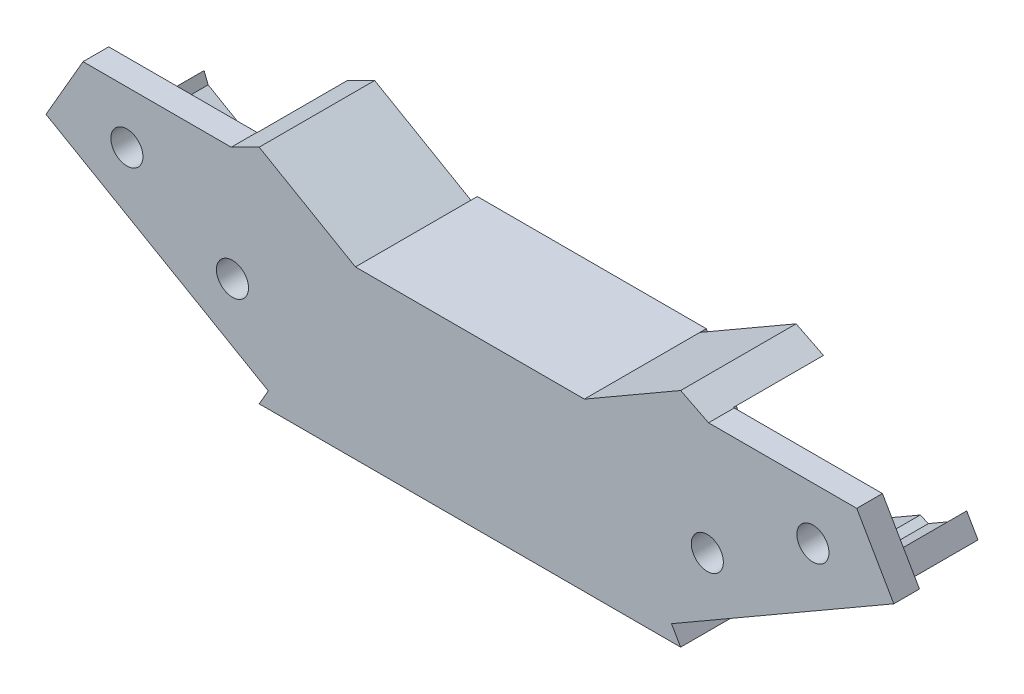
SolidWorks part; units mm, degrees
ref_plane "Alzado" through (0, 0, 0) normal (0, 0, 1) x (1, 0, 0)
ref_plane "Planta" through (0, 0, 0) normal (0, 1, 0) x (1, 0, 0)
ref_plane "Vista lateral" through (0, 0, 0) normal (1, 0, 0) x (0, 0, -1)
sketch "Croquis1" plane through (0, 0, 0) normal (0, 0, 1) x (1, 0, 0)
  line L0 (-8.9198, 0) -> (8.9198, 0)
  line L1 (-8.9198, 0) -> (0, -5.1498) construction
  line L2 (0, -5.1498) -> (8.9198, 0) construction
  line L3 (0, 0) -> (0, -5.1498) construction
  line L4 (8.9198, 0) -> (13.2499, 2.5) construction
  line L5 (8.9198, 0) -> (13.2499, -7.5) construction
  line L6 (8.9198, 0) -> (16.4198, -12.9904)
  line L7 (16.4198, -12.9904) -> (-16.4198, -12.9904)
  line L8 (-8.9198, 0) -> (-16.4198, -12.9904)
  arc A0 (-4.4599, -2.5749) -> (4.4599, -2.5749) centre (0, -5.1498) cw construction
  point P4 (0, 0)
  point P13 (0, -12.9904)
extrude "Saliente-Extruir1" add sketch "Croquis1" along normal blind 7.5
sketch "Croquis2" plane through (0, 0, 7.5) normal (0, 0, 1) x (1, 0, 0)
  line L5 (-18.5961, 3.2401) -> (-9.9358, -1.7599) construction
  line L6 (-8.9198, 0) -> (-16.4198, 4.3301)
  line L7 (-16.4198, 4.3301) -> (-18.5961, 3.2401)
  line L8 (16.4198, -12.9904) -> (8.9198, 0)
  line L9 (8.9198, 0) -> (-8.9198, 0)
  line L10 (-8.9198, 0) -> (-16.4198, -12.9904)
  line L11 (-16.4198, -12.9904) -> (16.4198, -12.9904)
  line L12 (16.4198, -12.9904) -> (15.7093, -11.7599)
  line L13 (8.9198, 0) -> (-8.9198, 0)
  line L14 (-15.7093, -11.7599) -> (-16.4198, -12.9904)
  line L15 (-16.4198, -12.9904) -> (16.4198, -12.9904)
  line L16 (-18.5961, 3.2401) -> (-30.1431, 3.2401)
  line L17 (-32.0563, -0.0737) -> (-27.0063, 8.6731) construction
  line L18 (-30.1431, 3.2401) -> (-33.0298, -1.7599)
  line L19 (-33.0298, -1.7599) -> (-15.7093, -11.7599)
  line L20 (0, 0) -> (0, -12.9904) construction
  line L21 (33.0298, -1.7599) -> (15.7093, -11.7599)
  line L22 (30.1431, 3.2401) -> (33.0298, -1.7599)
  line L23 (8.9198, 0) -> (16.4198, 4.3301)
  line L24 (16.4198, 4.3301) -> (18.5961, 3.2401)
  line L25 (18.5961, 3.2401) -> (30.1431, 3.2401)
  circle A0 centre (-26.7262, -0.8417) radius 1.25
  circle A1 centre (-18.499, -5.5917) radius 1.25
  circle A4 centre (18.499, -5.5917) radius 1.25
  circle A5 centre (26.7262, -0.8417) radius 1.25
  dimension "D1" = 0
extrude "Saliente-Extruir2" add sketch "Croquis2" along normal blind 2
sketch "Croquis3" plane through (0, 0, 7.5) normal (0, 0, -1) x (-1, 0, 0)
  line L0 (0, 0) -> (0, -12.9904) construction
  line L1 (-8.9198, 0) -> (8.9198, 0) construction
  line L2 (16.4198, -12.9904) -> (-16.4198, -12.9904) construction
  line L3 (-18.5497, 3.2633) -> (-16.4198, 4.3301)
  line L5 (-16.4198, 4.3301) -> (-8.9198, 0)
  line L6 (-8.9198, 0) -> (-9.9142, -1.7224)
  line L7 (-16.4198, -12.9904) -> (-8.9198, 0) construction
  line L8 (-9.9142, -1.7224) -> (-18.5497, 3.2633)
  line L9 (-30.3053, -3.3329) -> (-24.3696, -6.7599)
  line L10 (-15.7093, -11.7599) -> (-33.0298, -1.7599) construction
  line L11 (-24.3696, -6.7599) -> (-23.4906, -5.2375)
  line L12 (-23.4906, -5.2375) -> (-26.0816, -3.7415)
  line L13 (-26.0816, -3.7415) -> (-26.7297, -3.9939)
  line L14 (-26.7297, -3.9939) -> (-29.3966, -2.4542)
  line L15 (-29.3966, -2.4542) -> (-29.7113, -1.6459)
  line L16 (-29.7113, -1.6459) -> (-30.5903, -3.1684)
  line L17 (-30.5903, -3.1684) -> (-30.3053, -3.3329)
  line L18 (-21.3078, -8.5276) -> (-20.6608, -7.4069)
  line L19 (-20.6608, -7.4069) -> (-18.161, -8.8501)
  line L20 (-18.161, -8.8501) -> (-18.808, -9.9709)
  line L21 (-18.808, -9.9709) -> (-21.3078, -8.5276)
  line L22 (9.9142, -1.7224) -> (18.5497, 3.2633)
  line L23 (8.9198, 0) -> (9.9142, -1.7224)
  line L24 (16.4198, 4.3301) -> (8.9198, 0)
  line L25 (18.5497, 3.2633) -> (16.4198, 4.3301)
  line L26 (18.161, -8.8501) -> (18.808, -9.9709)
  line L27 (20.6608, -7.4069) -> (18.161, -8.8501)
  line L28 (21.3078, -8.5276) -> (20.6608, -7.4069)
  line L29 (18.808, -9.9709) -> (21.3078, -8.5276)
  line L30 (29.7113, -1.6459) -> (30.5903, -3.1684)
  line L31 (29.3966, -2.4542) -> (29.7113, -1.6459)
  line L32 (26.7297, -3.9939) -> (29.3966, -2.4542)
  line L33 (26.0816, -3.7415) -> (26.7297, -3.9939)
  line L34 (23.4906, -5.2375) -> (26.0816, -3.7415)
  line L35 (24.3696, -6.7599) -> (23.4906, -5.2375)
  line L36 (30.3053, -3.3329) -> (24.3696, -6.7599)
  line L37 (30.5903, -3.1684) -> (30.3053, -3.3329)
extrude "Saliente-Extruir3" add sketch "Croquis3" along normal blind 7
